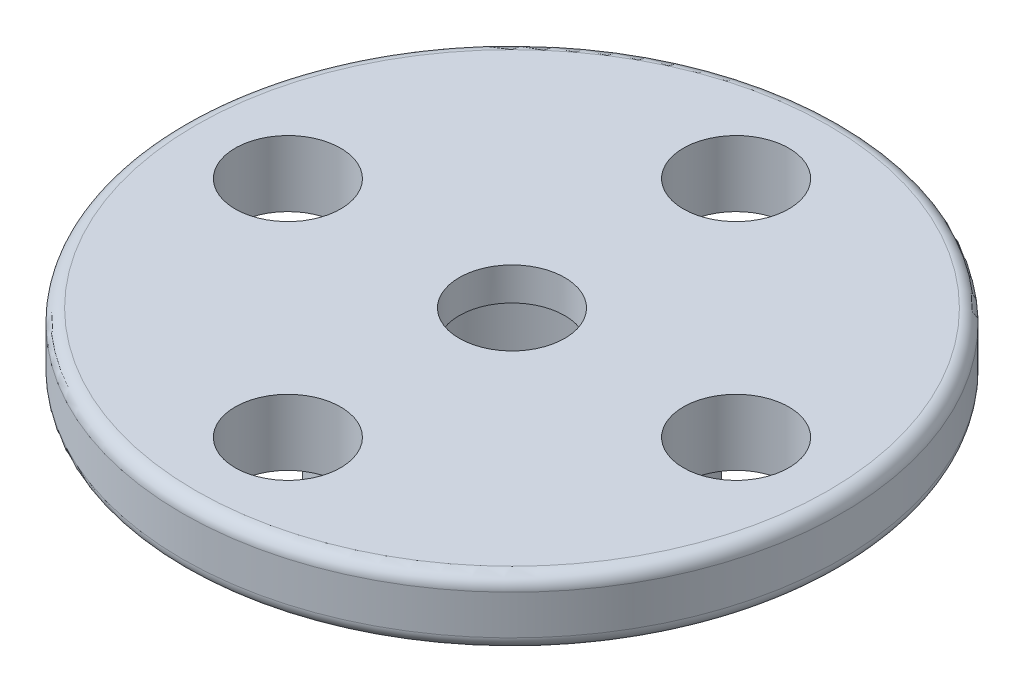
SolidWorks part; units mm, degrees
ref_plane "Front Plane" through (0, 0, 0) normal (0, 0, 1) x (1, 0, 0)
ref_plane "Top Plane" through (0, 0, 0) normal (0, 1, 0) x (1, 0, 0)
ref_plane "Right Plane" through (0, 0, 0) normal (1, 0, 0) x (0, 0, -1)
sketch "Sketch1" plane through (0, 0, 0) normal (0, 1, 0) x (1, 0, 0)
  circle A0 centre (0, 0) radius 10
  dimension "D1" = 20
extrude "Boss-Extrude1" add sketch "Sketch1" along normal blind 0.5
sketch "Sketch2" plane through (0, 0.5, 0) normal (0, 1, 0) x (1, 0, 0)
  circle A0 centre (0, 0) radius 10
  dimension "D1" = 20
extrude "Boss-Extrude2" add sketch "Sketch2" along normal blind 0.5
sketch "Sketch3" plane through (0, 1, 0) normal (0, 1, 0) x (1, 0, 0)
  circle A0 centre (0, 0) radius 10
  dimension "D1" = 20
extrude "Boss-Extrude3" add sketch "Sketch3" along normal blind 1
sketch "Sketch5" plane through (0, 2, 0) normal (0, 1, 0) x (1, 0, 0)
  circle A0 centre (0, 0) radius 1.6
  dimension "D1" = 3.2
extrude "Cut-Extrude2" cut sketch "Sketch5" against normal through all
sketch "Sketch8" plane through (0, 2, 0) normal (0, 1, 0) x (1, 0, 0)
  circle A0 centre (-6.8, 0) radius 1.6
  circle A1 centre (6.8, 0) radius 1.6
  circle A2 centre (0, 6.8) radius 1.6
  circle A3 centre (0, -6.8) radius 1.6
  dimension "D1" = 3.2
  dimension "D3" = 3.2
  dimension "D5" = 3.2
  dimension "D7" = 3.2
  dimension "D2" = 6.8
  dimension "D4" = 6.8
  dimension "D6" = 6.8
  dimension "D8" = 6.8
extrude "Cut-Extrude4" cut sketch "Sketch8" against normal blind 10
fillet "Fillet1" radius 0.4 2 edges at (0, 0, 10) (0, 2, 10)
sketch "Sketch9" plane through (0, 0, 0) normal (0, -1, 0) x (1, 0, 0)
  circle A0 centre (0, 0) radius 4.5
  circle A1 centre (0, 0) radius 3.5
  dimension "D1" = 9
  dimension "D2" = 7
extrude "Boss-Extrude4" add sketch "Sketch9" along normal blind 3
sketch "Sketch10" plane through (0, 0, 0) normal (0, -1, 0) x (1, 0, 0)
  circle A0 centre (0, 0) radius 3.5
extrude "Cut-Extrude5" cut sketch "Sketch10" against normal blind 1
fillet "Fillet3" radius 1.2 1 edges at (0, 1, -3.5)
